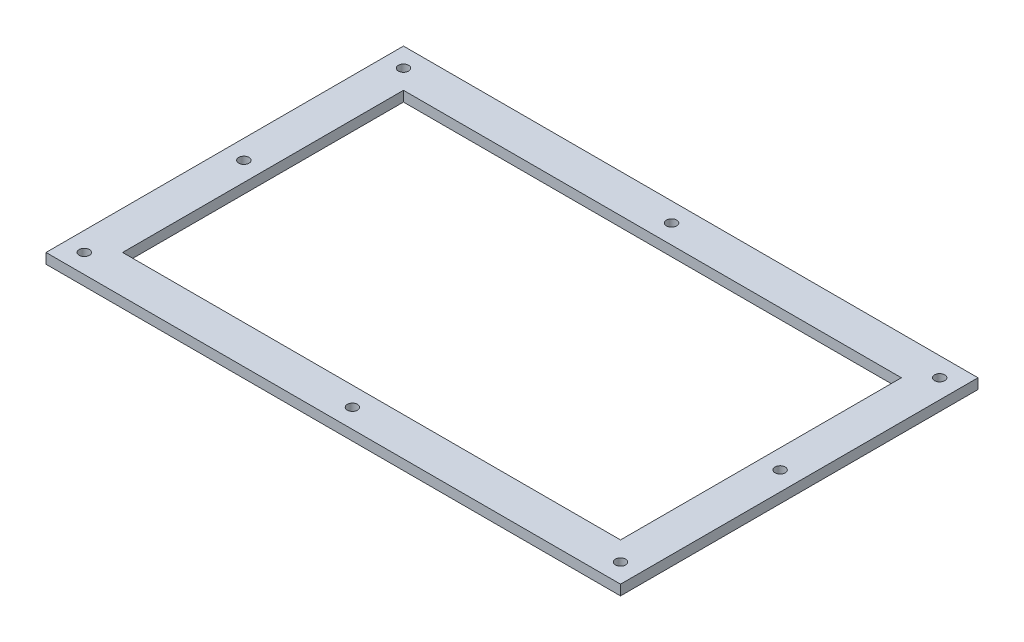
SolidWorks part; units mm, degrees
ref_plane "Front Plane" through (0, 0, 0) normal (0, 0, 1) x (1, 0, 0)
ref_plane "Top Plane" through (0, 0, 0) normal (0, 1, 0) x (1, 0, 0)
ref_plane "Right Plane" through (0, 0, 0) normal (1, 0, 0) x (0, 0, -1)
sketch "Sketch1" plane through (0, 0, 0) normal (0, 1, 0) x (1, 0, 0)
  line L1 (-85, -70) -> (140, -70)
  line L3 (-85, 70) -> (140, 70)
  line L4 (140, -70) -> (140, 70)
  line L17 (-85, -70) -> (-85, 70)
  line L25 (-70, 55) -> (125, 55)
  line L26 (-70, 55) -> (-70, -55)
  line L27 (-70, -55) -> (125, -55)
  line L28 (125, 55) -> (125, -55)
  circle A4 centre (-77.5, -62.5) radius 2
  circle A5 centre (-77.5, 62.5) radius 2
  circle A6 centre (132.5, 62.5) radius 2
  circle A7 centre (132.5, -62.5) radius 2
  circle A8 centre (27.5, -62.5) radius 2
  circle A9 centre (27.5, 62.5) radius 2
  circle A10 centre (-77.5, 0) radius 2
  circle A11 centre (132.5, 0) radius 2
  point P14 (0, 0)
  point P19 (0, 0)
  point P20 (0, 0)
extrude "Boss-Extrude1" add sketch "Sketch1" along normal blind 4
